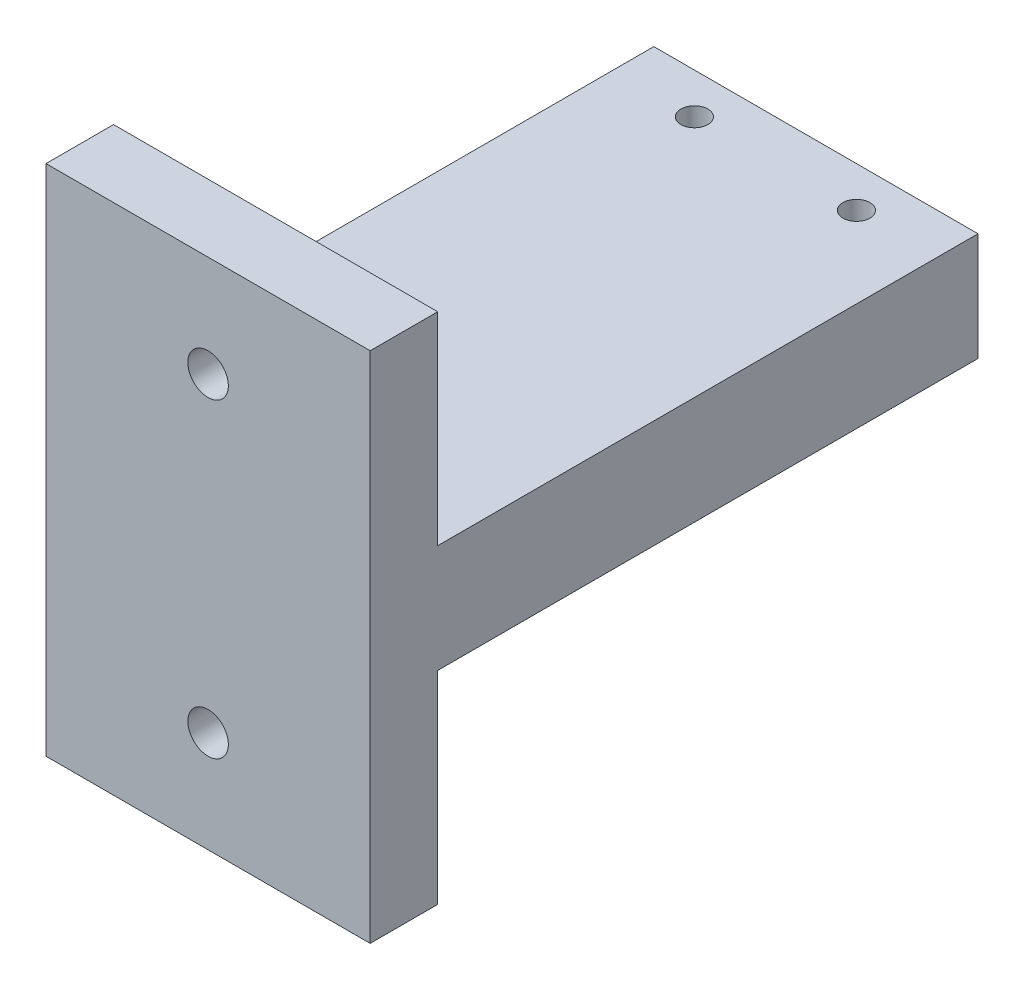
SolidWorks part; units mm, degrees
ref_plane "Front Plane" through (0, 0, 0) normal (0, 0, 1) x (1, 0, 0)
ref_plane "Top Plane" through (0, 0, 0) normal (0, 1, 0) x (1, 0, 0)
ref_plane "Right Plane" through (0, 0, 0) normal (1, 0, 0) x (0, 0, -1)
sketch "Sketch2" plane through (0, 0, 0) normal (0, 1, 0) x (1, 0, 0)
  line L1 (-19.197, 24.2503) -> (4.803, 24.2503)
  line L2 (-19.197, 24.2503) -> (-19.197, -20.7497)
  line L3 (-19.197, -20.7497) -> (4.803, -20.7497)
  line L4 (4.803, 24.2503) -> (4.803, -20.7497)
extrude "Boss-Extrude1" add sketch "Sketch2" along normal blind 8
sketch "Sketch5" plane through (0, 8, 0) normal (0, 1, 0) x (1, 0, 0)
  line L0 (4.803, -20.7497) -> (4.803, 24.2503) construction
  line L1 (-19.197, -20.7497) -> (4.803, -20.7497)
  line L2 (-19.197, -20.7497) -> (-19.197, -15.7497)
  line L3 (-19.197, -15.7497) -> (4.803, -15.7497)
  line L4 (4.803, -20.7497) -> (4.803, -15.7497)
extrude "Boss-Extrude2" add sketch "Sketch5" along normal blind 15
sketch "Sketch6" plane through (0, 0, 0) normal (0, -1, 0) x (1, 0, 0)
  line L0 (-19.197, -24.2503) -> (-19.197, 20.7497) construction
  line L1 (4.803, 20.7497) -> (-19.197, 20.7497)
  line L2 (4.803, 20.7497) -> (4.803, 15.7497)
  line L3 (4.803, 15.7497) -> (-19.197, 15.7497)
  line L4 (-19.197, 20.7497) -> (-19.197, 15.7497)
extrude "Boss-Extrude3" add sketch "Sketch6" along normal blind 15
sketch "Sketch7" plane through (0, 0, 15.7497) normal (0, 0, -1) x (-1, 0, 0)
  circle A0 centre (7.197, 15.5) radius 1.5
  circle A1 centre (7.197, -7.5) radius 1.5
extrude "Cut-Extrude1" cut sketch "Sketch7" against normal blind 5
sketch "Sketch8" plane through (0, 8, 0) normal (0, 1, 0) x (1, 0, 0)
  circle A0 centre (-13.197, 21.2503) radius 1
  circle A1 centre (-1.197, 21.2503) radius 1
extrude "Cut-Extrude2" cut sketch "Sketch8" against normal blind 4
